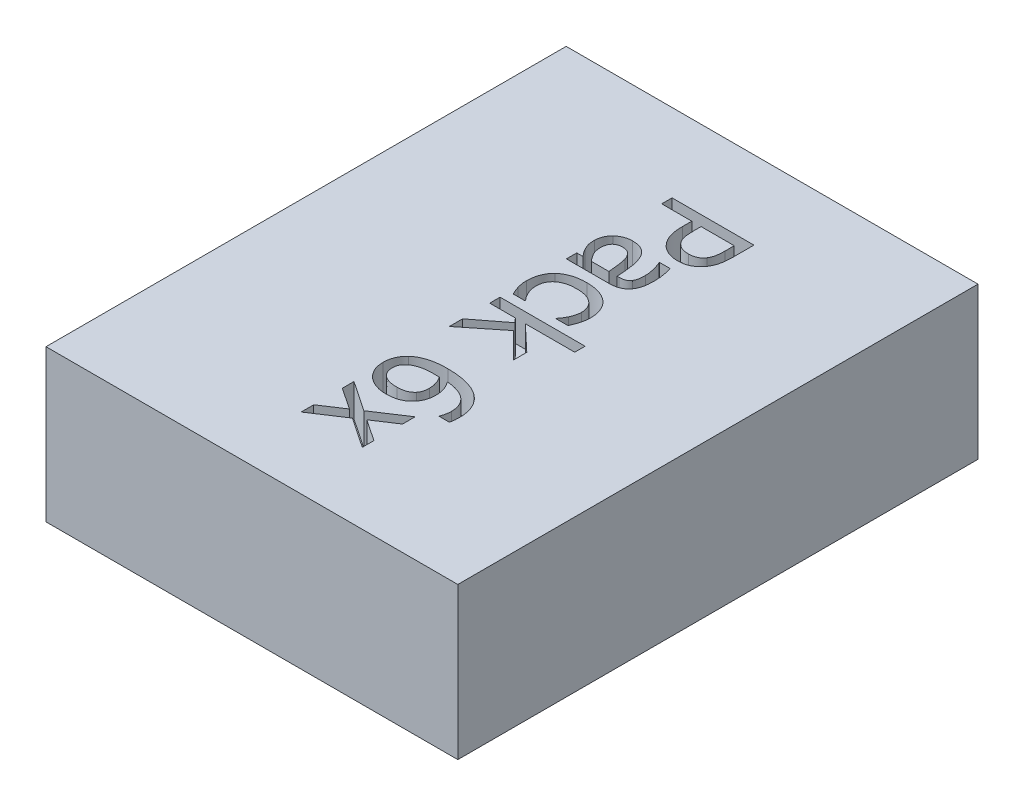
SolidWorks part; units mm, degrees
material "Rubber"
ref_plane "Спереди" through (0, 0, 0) normal (0, 0, 1) x (1, 0, 0)
ref_plane "Сверху" through (0, 0, 0) normal (0, 1, 0) x (1, 0, 0)
ref_plane "Справа" through (0, 0, 0) normal (1, 0, 0) x (0, 0, -1)
sketch "Sketch1" plane through (0, 0, 0) normal (0, 0, 1) x (1, 0, 0)
  line L1 (-19, -7) -> (19, -7)
  line L2 (-19, -7) -> (-19, 7)
  line L3 (-19, 7) -> (19, 7)
  line L4 (19, -7) -> (19, 7)
  line L5 (-19, -7) -> (19, 7) construction
  line L6 (-19, 7) -> (19, -7) construction
  point P0 (0, 0)
  dimension "D1" = 38
  dimension "D2" = 14
extrude "Boss-Extrude1" add sketch "Sketch1" along normal blind 48
sketch "Sketch2" plane through (0, 7, 0) normal (0, 1, 0) x (1, 0, 0)
  line L0 (-2.0076, 0) -> (-2.0076, -48) construction
  line L1 (19, 0) -> (-19, 0) construction
  line L2 (19, -48) -> (-19, -48) construction
  text T0 "Pack 6x" font "Tahoma" height in points 28
extrude "Cut-Extrude1" cut sketch "Sketch2" against normal blind 3
equation "\"SALT_BATTERY_THICKNESS\"= 8mm"
